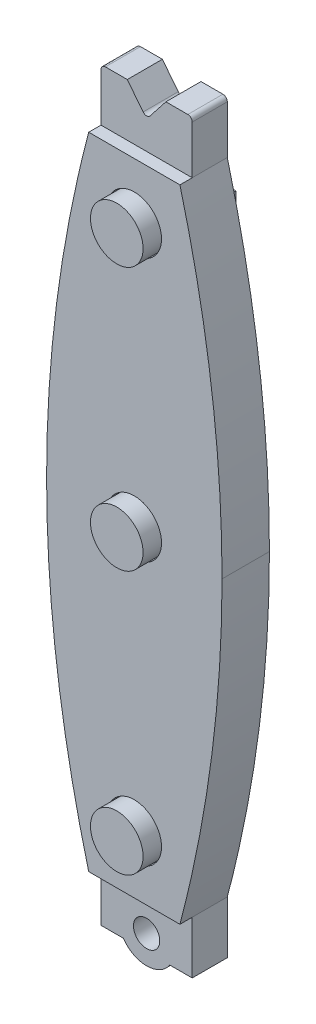
SolidWorks part; units mm, degrees
ref_plane "Front Plane" through (0, 0, 0) normal (0, 0, 1) x (1, 0, 0)
ref_plane "Top Plane" through (0, 0, 0) normal (0, 1, 0) x (1, 0, 0)
ref_plane "Right Plane" through (0, 0, 0) normal (1, 0, 0) x (0, 0, -1)
sketch "Sketch1" plane through (0, 0, 0) normal (0, 0, 1) x (1, 0, 0)
  line L1 (-33.062, 41.9494) -> (-7.662, 41.9494)
  line L2 (-33.062, 41.9494) -> (-33.062, -50.7606)
  line L3 (-33.062, -50.7606) -> (-7.662, -50.7606)
  line L4 (-7.662, 41.9494) -> (-7.662, -50.7606)
  dimension "D1" = 92.71
  dimension "D2" = 25.4
extrude "Boss-Extrude1" add sketch "Sketch1" along normal blind 5.08
sketch "Sketch3" plane through (0, -50.7606, 0) normal (0, -1, 0) x (1, 0, 0)
  line L0 (-7.662, 0) -> (-33.062, 5.08) construction
  line L1 (-33.062, 0) -> (-7.662, 0) construction
  line L2 (-13.758, 5.08) -> (-26.966, 5.08)
  line L3 (-13.758, 5.08) -> (-13.758, 0)
  line L4 (-13.758, 0) -> (-26.966, 0)
  line L5 (-26.966, 5.08) -> (-26.966, 0)
  line L6 (-13.758, 5.08) -> (-26.966, 0) construction
  line L7 (-13.758, 0) -> (-26.966, 5.08) construction
  point P4 (-20.362, 2.54)
  dimension "D1" = 13.208
extrude "Boss-Extrude3" add sketch "Sketch3" along normal blind 11.938
sketch "Sketch5" plane through (0, 0, 5.08) normal (0, 0, 1) x (1, 0, 0)
  line L0 (-23.7221, -58.3806) -> (-26.966, -58.3806)
  line L1 (-33.062, 41.9494) -> (-33.062, -50.7606) construction
  line L2 (-13.758, -62.6986) -> (-26.966, -62.6986) construction
  line L4 (-13.758, -62.6986) -> (-13.758, -58.3806)
  line L5 (-13.758, -58.3806) -> (-17.0019, -58.3806)
  line L6 (-13.758, -50.7606) -> (-7.662, -50.7606) construction
  line L8 (-26.966, -62.6986) -> (-26.966, -58.3806)
  line L9 (-13.758, -62.6986) -> (-26.966, -62.6986)
  circle A0 centre (-20.362, -56.0946) radius 1.905
  arc A1 (-23.7221, -58.3806) -> (-17.0019, -58.3806) centre (-20.362, -56.0946) ccw
  dimension "D2" = 3.81
  dimension "D3" = 8.128
  dimension "D4" = 7.62
extrude "Cut-Extrude2" cut sketch "Sketch5" against normal through all
sketch "Sketch7" plane through (0, 0, 5.08) normal (0, 0, 1) x (1, 0, 0)
  line L1 (-7.662, -50.7606) -> (-33.062, -50.7606)
  line L2 (-7.662, -50.7606) -> (-7.662, 41.9494)
  line L3 (-7.662, 41.9494) -> (-33.062, 41.9494)
  line L4 (-33.062, -50.7606) -> (-33.062, 41.9494)
extrude "Boss-Extrude4" add sketch "Sketch7" along normal blind 1.778
sketch "Sketch8" plane through (0, 0, 6.858) normal (0, 0, 1) x (1, 0, 0)
  line L0 (-33.062, -50.7606) -> (-7.662, -50.7606) construction
  circle A0 centre (-20.362, -42.3786) radius 3.937
  circle A1 centre (-20.362, -4.2786) radius 3.937
  circle A2 centre (-20.362, 33.8214) radius 3.937
  dimension "D1" = 7.874
  dimension "D2" = 8.382
  dimension "D3" = 3
extrude "Cut-Extrude3" cut sketch "Sketch8" against normal blind 1.27
sketch "Sketch10" plane through (0, 0, 5.588) normal (0, 0, 1) x (1, 0, 0)
  circle A0 centre (-20.362, -42.3786) radius 3.81
  circle A1 centre (-20.362, -4.2786) radius 3.81
  circle A2 centre (-20.362, 33.8214) radius 3.81
  dimension "D1" = 7.62
  dimension "D2" = 3
extrude "Boss-Extrude5" add sketch "Sketch10" along normal blind 3.81
sketch "Sketch11" plane through (0, 41.9494, 0) normal (0, 1, 0) x (1, 0, 0)
  line L0 (-20.362, 0) -> (-20.362, -6.858) construction
  line L1 (-7.662, 0) -> (-33.062, 0) construction
  line L2 (-7.662, -6.858) -> (-33.062, -6.858) construction
  line L4 (-13.758, -5.08) -> (-26.966, -5.08)
  line L5 (-13.758, -5.08) -> (-13.758, 0)
  line L6 (-13.758, 0) -> (-26.966, 0)
  line L7 (-26.966, -5.08) -> (-26.966, 0)
  line L8 (-13.758, -5.08) -> (-26.966, 0) construction
  line L9 (-13.758, 0) -> (-26.966, -5.08) construction
  point P6 (-20.362, -2.54)
  dimension "D1" = 13.208
  dimension "D2" = 5.08
  dimension "D3" = 0
extrude "Boss-Extrude6" add sketch "Sketch11" along normal blind 7.62
sketch "Sketch12" plane through (0, 0, 5.08) normal (0, 0, 1) x (1, 0, 0)
  line L0 (-26.966, 46.0134) -> (-13.758, 46.0134) construction
  line L1 (-26.966, 49.5694) -> (-26.966, 41.9494) construction
  line L2 (-13.758, 49.5694) -> (-13.758, 41.9494) construction
  line L3 (-23.156, 49.5694) -> (-23.156, 41.9494) construction
  line L4 (-26.966, 49.5694) -> (-13.758, 49.5694) construction
  line L5 (-26.966, 41.9494) -> (-13.758, 41.9494) construction
  line L6 (-17.568, 49.5694) -> (-17.568, 41.9494) construction
  line L7 (-7.662, 41.9494) -> (-33.062, 41.9494) construction
  line L8 (-20.362, 49.5694) -> (-20.362, 41.9494) construction
  line L9 (-23.156, 49.5694) -> (-20.362, 46.0134)
  line L10 (-20.362, 46.0134) -> (-17.568, 49.5694)
  line L11 (-17.568, 49.5694) -> (-23.156, 49.5694)
  dimension "D1" = 2.794
  dimension "D2" = 3.556
  dimension "D3" = 2.794
extrude "Cut-Extrude4" cut sketch "Sketch12" against normal through all
fillet "Fillet1" radius 0.635 3 edges at (-26.966, 49.5694, 2.54) (-20.362, 46.0134, 2.54) (-13.758, 49.5694, 2.54)
sketch "Sketch14" plane through (0, 0, 6.858) normal (0, 0, 1) x (1, 0, 0)
  line L0 (-7.662, -50.7606) -> (-7.662, 41.9494) construction
  line L1 (-33.062, 41.9494) -> (-33.062, -50.7606) construction
  line L2 (-13.758, 41.9494) -> (-7.662, 41.9494)
  line L3 (-7.662, 41.9494) -> (-7.662, -4.4056)
  line L4 (-33.062, -4.4056) -> (-33.062, 41.9494)
  line L6 (-33.062, 41.9494) -> (-26.966, 41.9494)
  spline S0 degree 2 poles (-13.758, 41.9494) (-7.662, 18.7719) (-7.662, -4.4056) knots 0 0 0 0.5 0.5 0.5
  spline S1 degree 2 poles (-26.966, 41.9494) (-33.062, 18.7719) (-33.062, -4.4056) knots 0 0 0 0.5 0.5 0.5
extrude "Cut-Extrude7" cut sketch "Sketch14" against normal blind 7.62
sketch "Sketch16" plane through (0, 0, 6.858) normal (0, 0, 1) x (1, 0, 0)
  line L1 (-33.062, -4.4056) -> (-33.062, -50.7606)
  line L2 (-33.062, -50.7606) -> (-26.966, -50.7606)
  line L3 (-7.662, -4.4056) -> (-7.662, -50.7606)
  line L4 (-7.662, -50.7606) -> (-13.758, -50.7606)
  spline S0 degree 2 poles (-13.758, -50.7606) (-7.662, -27.5831) (-7.662, -4.4056) knots 0 0 0 0.5 0.5 0.5
  spline S1 degree 2 poles (-33.062, -4.4056) (-33.062, -27.5831) (-26.966, -50.7606) knots 0.5 0.5 0.5 1 1 1
extrude "Cut-Extrude8" cut sketch "Sketch16" against normal through all
sketch "Sketch17" plane through (0, 0, 0) normal (0, 0, -1) x (-1, 0, 0)
  line L0 (7.662, -4.4056) -> (33.062, -4.4056) construction
  line L2 (14.012, -45.6806) -> (26.712, -45.6806)
  line L3 (14.012, -45.6806) -> (14.012, 36.8694)
  line L4 (14.012, 36.8694) -> (26.712, 36.8694)
  line L5 (26.712, -45.6806) -> (26.712, 36.8694)
  line L6 (14.012, -45.6806) -> (26.712, 36.8694) construction
  line L7 (14.012, 36.8694) -> (26.712, -45.6806) construction
  point P4 (20.362, -4.4056)
  dimension "D1" = 82.55
  dimension "D2" = 12.7
extrude "Boss-Extrude7" add sketch "Sketch17" along normal blind 1.524
